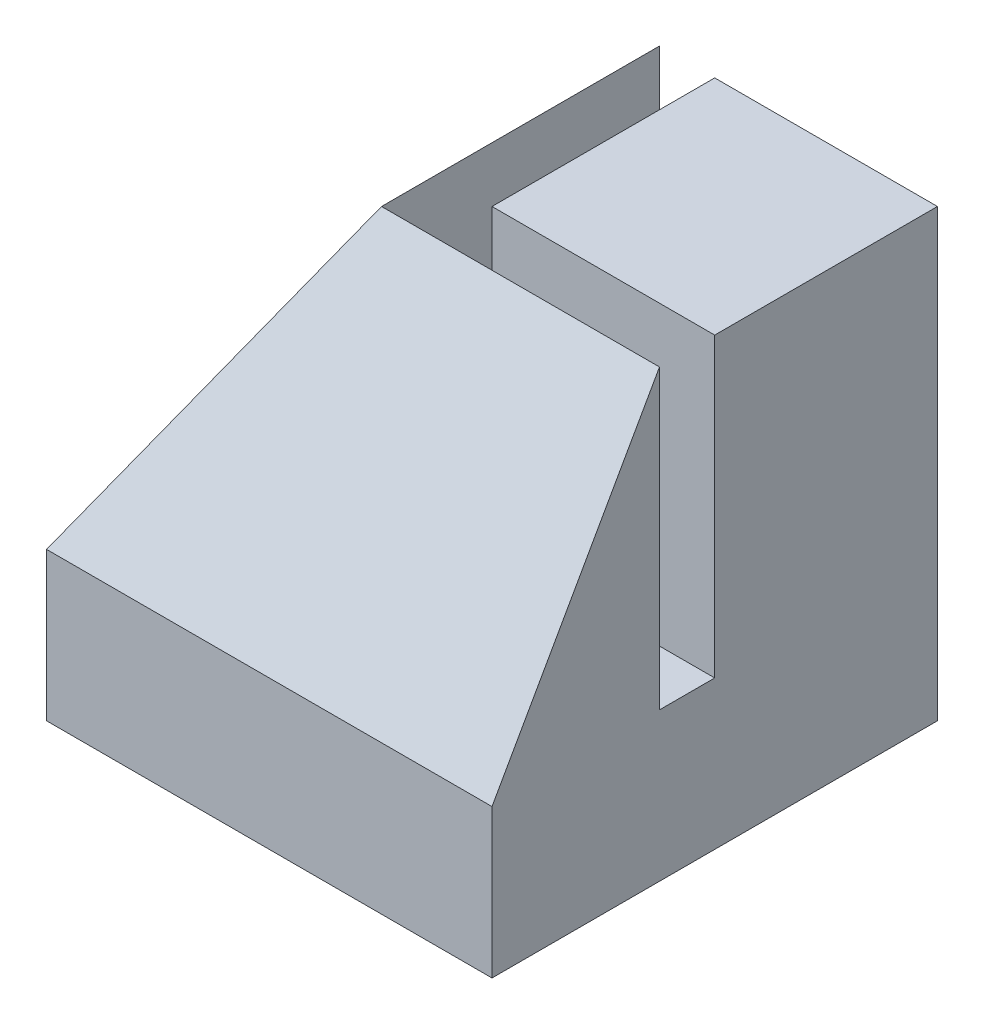
SolidWorks part; units mm, degrees
ref_plane "Front Plane" through (0, 0, 0) normal (0, 0, 1) x (1, 0, 0)
ref_plane "Top Plane" through (0, 0, 0) normal (0, 1, 0) x (1, 0, 0)
ref_plane "Right Plane" through (0, 0, 0) normal (1, 0, 0) x (0, 0, -1)
sketch "Sketch1" plane through (0, 0, 0) normal (0, 1, 0) x (1, 0, 0)
  line L1 (-9.525, -9.525) -> (9.525, -9.525)
  line L2 (-9.525, -9.525) -> (-9.525, 9.525)
  line L3 (-9.525, 9.525) -> (9.525, 9.525)
  line L4 (9.525, -9.525) -> (9.525, 9.525)
  line L5 (-9.525, -9.525) -> (9.525, 9.525) construction
  line L6 (-9.525, 9.525) -> (9.525, -9.525) construction
  point P0 (0, 0)
  dimension "D1" = 19.05
  dimension "D2" = 19.05
extrude "Body" add sketch "Sketch1" along normal blind 19.05
sketch "Sketch2" plane through (0, 19.05, 0) normal (0, 1, 0) x (1, 0, 0)
  line L0 (-2.3622, 9.525) -> (-2.3622, -2.3622)
  line L1 (9.525, 9.525) -> (-9.525, 9.525) construction
  line L2 (-2.3622, -2.3622) -> (9.525, -2.3622)
  line L3 (9.525, -9.525) -> (9.525, 9.525) construction
  line L4 (9.525, -2.3622) -> (9.525, 0)
  line L5 (9.525, 0) -> (0, 0)
  line L6 (0, 0) -> (0, 9.525)
  line L7 (0, 9.525) -> (-2.3622, 9.525)
  dimension "D1" = 2.3622
  dimension "D3" = 2.3622
extrude "Slot" cut sketch "Sketch2" against normal blind 12.7
sketch "Sketch3" plane through (0, 0, 9.525) normal (0, 0, 1) x (1, 0, 0)
  line L0 (-2.3622, 19.05) -> (-9.525, 19.05)
  line L1 (-9.525, 19.05) -> (-9.525, 6.35)
  line L2 (-9.525, 19.05) -> (-9.525, 0) construction
  line L3 (-9.525, 6.35) -> (-2.3622, 19.05)
extrude "Bevel Left" cut sketch "Sketch3" against normal blind 19.05
sketch "Sketch4" plane through (9.525, 0, 0) normal (1, 0, 0) x (0, 0, -1)
  line L0 (-2.3622, 19.05) -> (-9.525, 6.35)
  line L1 (-9.525, 6.35) -> (-9.525, 19.05)
  line L2 (-9.525, 19.05) -> (-2.3622, 19.05)
extrude "Bevel Right" cut sketch "Sketch4" against normal blind 19.05
